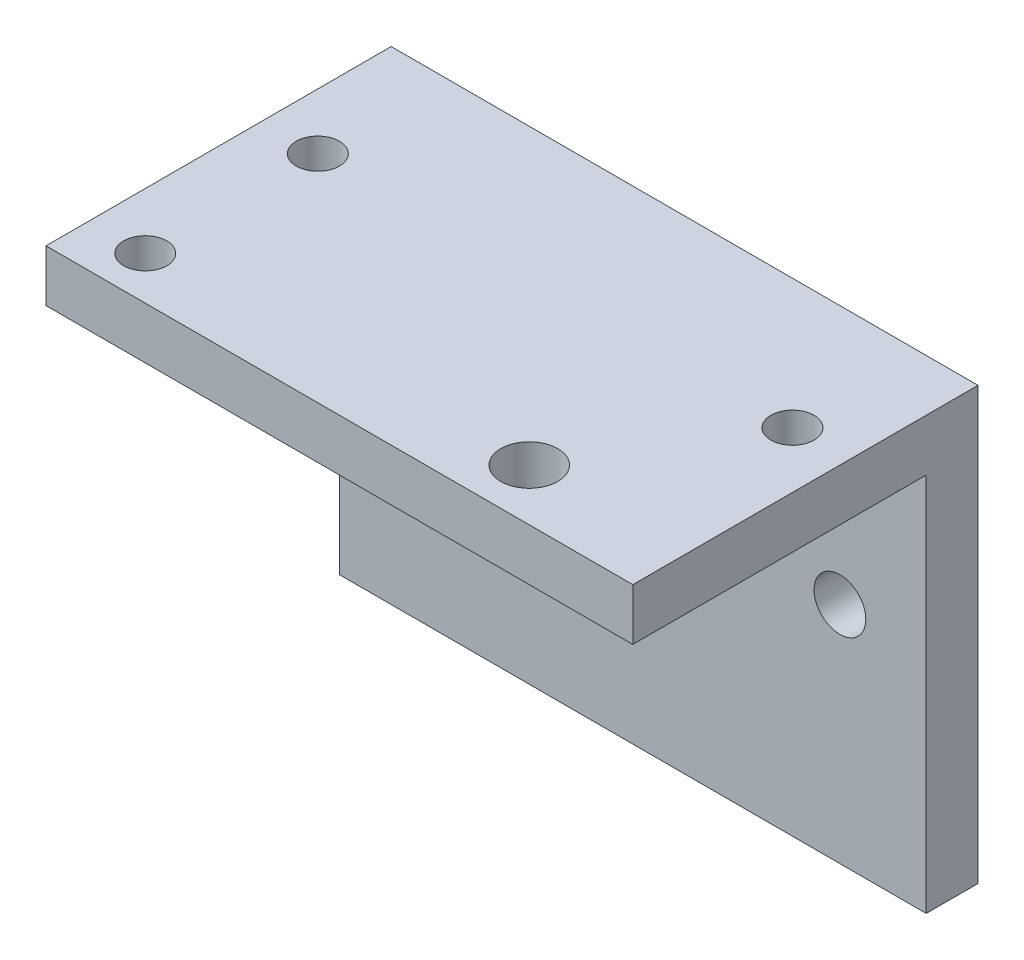
SolidWorks part; units mm, degrees
material "6061 合金"
ref_plane "前视基准面" through (0, 0, 0) normal (0, 0, 1) x (1, 0, 0)
ref_plane "上视基准面" through (0, 0, 0) normal (0, 1, 0) x (1, 0, 0)
ref_plane "右视基准面" through (0, 0, 0) normal (1, 0, 0) x (0, 0, -1)
sketch "草图1" plane through (0, 0, 0) normal (0, 1, 0) x (1, 0, 0)
  line L0 (0, 0) -> (0, 40) construction
  line L1 (-34, 40) -> (34, 40)
  line L2 (-34, 40) -> (-34, 0)
  line L3 (-34, 0) -> (34, 0)
  line L4 (34, 40) -> (34, 0)
  line L5 (0, 0) -> (51.5608, 0) construction
  line L6 (-27.5, 25) -> (27.5, 25) construction
  line L7 (-27.5, 25) -> (-27.5, 5) construction
  line L8 (27.5, 25) -> (27.5, 5) construction
  line L9 (-27.5, 5) -> (27.5, 5) construction
  line L10 (-27.5, 25) -> (27.5, 5) construction
  line L11 (27.5, 25) -> (-27.5, 5) construction
  circle A0 centre (-27.5, 25) radius 2.5
  circle A1 centre (27.5, 25) radius 2.5
  circle A2 centre (-27.5, 5) radius 2.5
  point P9 (0, 15)
  dimension "D7" = 5
  dimension "D8" = 5
  dimension "D9" = 5
  dimension "D1" = 68
  dimension "D2" = 40
  dimension "D3" = 55
  dimension "D4" = 20
  dimension "D5" = 15
extrude "凸台-拉伸1" add sketch "草图1" along normal blind 6
sketch "草图3" plane through (0, 6, 0) normal (0, 1, 0) x (1, 0, 0)
  line L0 (34, 40) -> (-34, 40) construction
  line L1 (-34, 40) -> (34, 40)
  line L2 (-34, 40) -> (-34, 34)
  line L3 (-34, 34) -> (34, 34)
  line L4 (34, 40) -> (34, 34)
  line L5 (-34, 40) -> (-34, 0) construction
  dimension "D2" = 68
  dimension "D3" = 6
extrude "凸台-拉伸2" add sketch "草图3" against normal blind 50
sketch "草图4" plane through (0, 0, -34) normal (0, 0, 1) x (1, 0, 0)
  line L0 (0, -45) -> (0, 0) construction
  line L2 (0, -18) -> (24, -18) construction
  line L3 (34, 6) -> (-34, 6) construction
  line L5 (-34, 0) -> (34, 0) construction
  circle A0 centre (0, -18) radius 8
  circle A1 centre (24, -18) radius 3
  circle A2 centre (-24, -18) radius 3
  dimension "D1" = 16
  dimension "D3" = 6
  dimension "D2" = 24
  dimension "D4" = 24
extrude "切除-拉伸1" cut sketch "草图4" against normal up to next
sketch "草图5" plane through (0, 0, 0) normal (0, -1, 0) x (1, 0, 0)
  line L2 (-34, 0) -> (34, 0) construction
  line L4 (34, 0) -> (34, -34) construction
  circle A0 centre (16, -6) radius 3.3
  dimension "D3" = 6.6
  dimension "D1" = 6
  dimension "D2" = 18
extrude "切除-拉伸2" cut sketch "草图5" against normal blind 10
